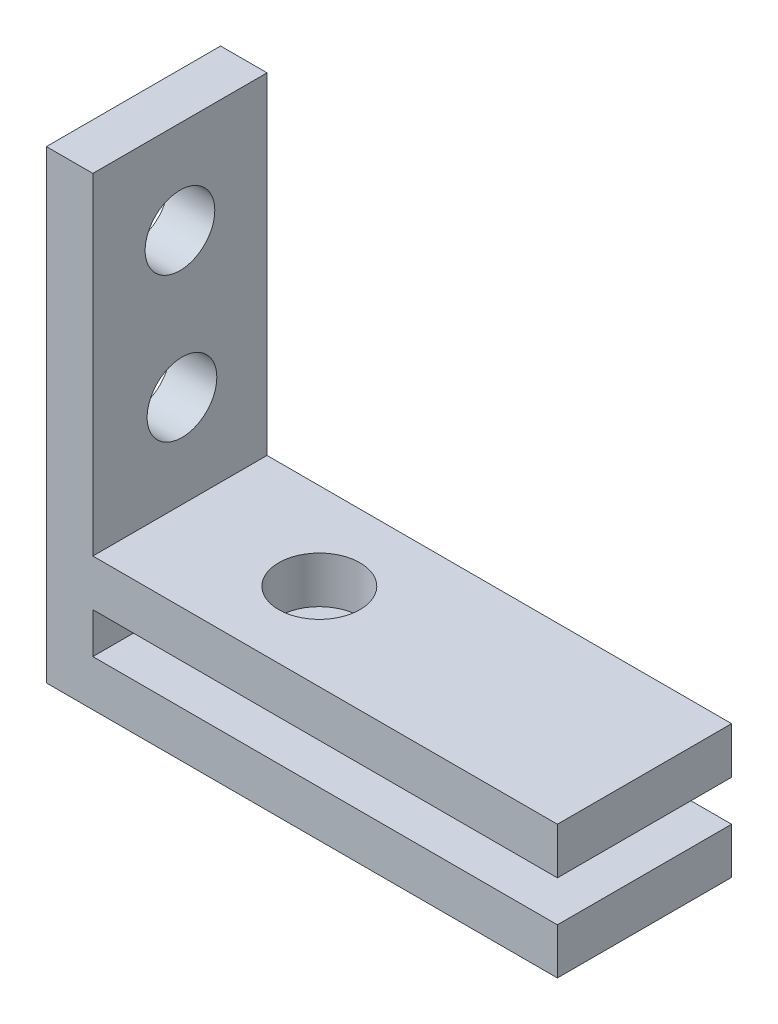
SolidWorks part; units mm, degrees
ref_plane "Front Plane" through (0, 0, 0) normal (0, 0, 1) x (1, 0, 0)
ref_plane "Top Plane" through (0, 0, 0) normal (0, 1, 0) x (1, 0, 0)
ref_plane "Right Plane" through (0, 0, 0) normal (1, 0, 0) x (0, 0, -1)
sketch "Sketch1" plane through (0, 0, 0) normal (1, 0, 0) x (0, 0, -1)
  line L1 (-0.7404, 9.0244) -> (6.7596, 9.0244)
  line L2 (-0.7404, 9.0244) -> (-0.7404, -10.9756)
  line L3 (-0.7404, -10.9756) -> (6.7596, -10.9756)
  line L4 (6.7596, 9.0244) -> (6.7596, -10.9756)
  dimension "D1" = 20
  dimension "D2" = 7.5
extrude "Boss-Extrude2" add sketch "Sketch1" along normal blind 2
sketch "Sketch2" plane through (2, 0, 0) normal (1, 0, 0) x (0, 0, -1)
  line L0 (-0.7404, 9.0244) -> (-0.7404, -10.9756) construction
  line L1 (6.7596, -10.9756) -> (-0.7404, -10.9756)
  line L2 (6.7596, -10.9756) -> (6.7596, -8.9921)
  line L3 (6.7596, -8.9921) -> (-0.7404, -8.9921)
  line L4 (-0.7404, -10.9756) -> (-0.7404, -8.9921)
extrude "Boss-Extrude3" add sketch "Sketch2" along normal blind 20
sketch "Sketch3" plane through (2, 0, 0) normal (1, 0, 0) x (0, 0, -1)
  line L0 (6.7596, -8.9921) -> (6.7596, 9.0244) construction
  line L1 (-0.7404, -8.9921) -> (6.7596, -8.9921)
  line L2 (-0.7404, -8.9921) -> (-0.7404, -7.2421)
  line L3 (-0.7404, -7.2421) -> (6.7596, -7.2421)
  line L4 (6.7596, -8.9921) -> (6.7596, -7.2421)
  line L6 (-0.7404, -7.2421) -> (6.7596, -7.2421)
  line L7 (-0.7404, -7.2421) -> (-0.7404, -5.2421)
  line L8 (-0.7404, -5.2421) -> (6.7596, -5.2421)
  line L9 (6.7596, -7.2421) -> (6.7596, -5.2421)
  line M5 (6.7596, -8.9921) -> (6.7596, 9.0244)
  line M7 (-0.7404, 9.0244) -> (-0.7404, -8.9921)
  dimension "D1" = 2
  dimension "D2" = 1.75
extrude "Boss-Extrude4" add sketch "Sketch3" along normal blind 20 contours L8 L3 M7 M5
sketch "Sketch5" plane through (2, 0, 0) normal (1, 0, 0) x (0, 0, -1)
  line L0 (6.7596, -5.2421) -> (6.7596, 9.0244) construction
  line L2 (6.7596, 9.0244) -> (-0.7404, 9.0244) construction
  line L5 (-0.7404, -5.2421) -> (6.7596, -5.2421) construction
  circle A0 centre (3.0096, 5.0244) radius 1.5
  circle A1 centre (3.0965, -1.2421) radius 1.5
  dimension "D1" = 3.75
  dimension "D2" = 4
  dimension "D3" = 4
extrude "Cut-Extrude1" cut sketch "Sketch5" against normal blind 20
sketch "Sketch6" plane through (0, -5.2421, 0) normal (0, 1, 0) x (1, 0, 0)
  line L0 (22, 6.7596) -> (2, 6.7596) construction
  line L1 (2, -0.7404) -> (2, 6.7596) construction
  circle A1 centre (8, 3.0096) radius 1.75
  dimension "D3" = 3.75
  dimension "D4" = 6
extrude "Cut-Extrude2" cut sketch "Sketch6" against normal blind 10
